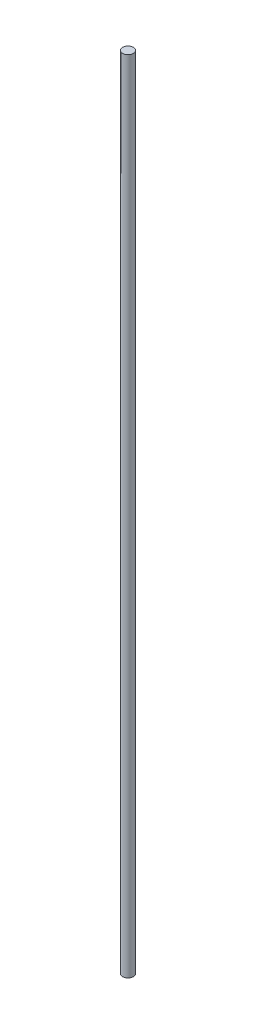
SolidWorks part; units mm, degrees
ref_plane "Front Plane" through (0, 0, 0) normal (0, 0, 1) x (1, 0, 0)
ref_plane "Top Plane" through (0, 0, 0) normal (0, 1, 0) x (1, 0, 0)
ref_plane "Right Plane" through (0, 0, 0) normal (1, 0, 0) x (0, 0, -1)
sketch "Sketch1" plane through (0, 0, 0) normal (0, 1, 0) x (1, 0, 0)
  circle A0 centre (0, 0) radius 4
  dimension "D1" = 8
extrude "Boss-Extrude1" add sketch "Sketch1" along normal blind 600 contours A0
